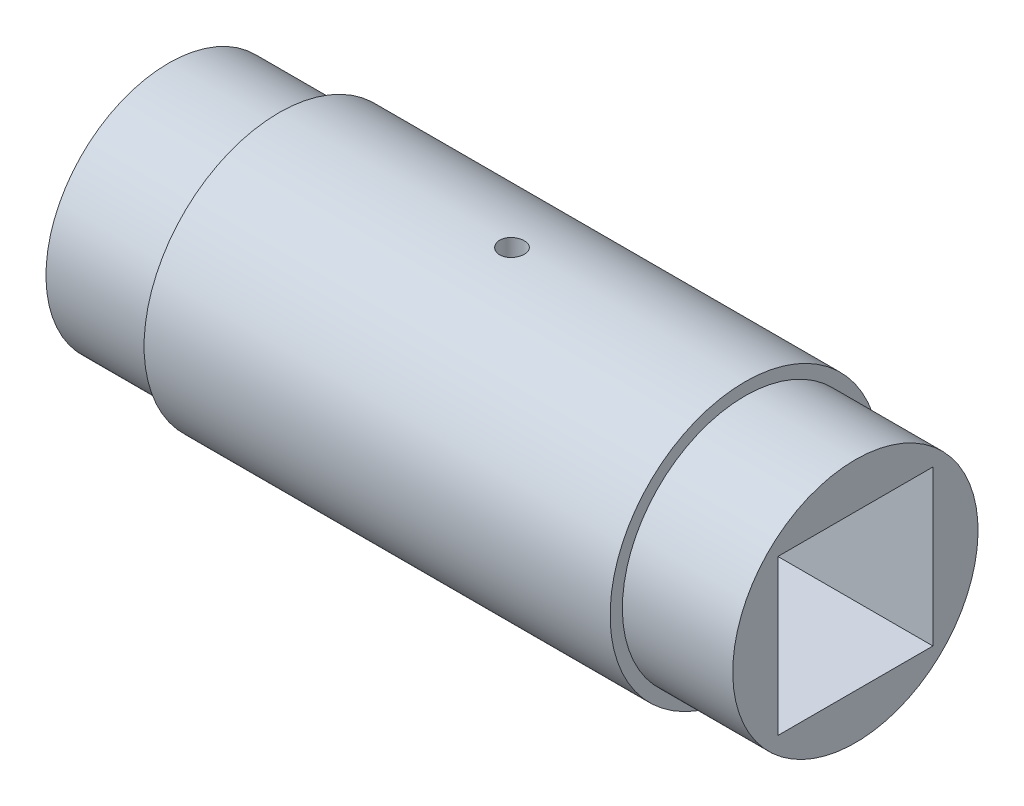
SolidWorks part; units mm, degrees
ref_plane "Front Plane" through (0, 0, 0) normal (0, 0, 1) x (1, 0, 0)
ref_plane "Top Plane" through (0, 0, 0) normal (0, 1, 0) x (1, 0, 0)
ref_plane "Right Plane" through (0, 0, 0) normal (1, 0, 0) x (0, 0, -1)
sketch "Sketch1" plane through (0, 0, 0) normal (0, 0, 1) x (1, 0, 0)
  line L1 (-9.5, 5.5) -> (9.5, 5.5)
  line L2 (-9.5, 5.5) -> (-9.5, 5)
  line L3 (-14, 0) -> (14, 0)
  line L4 (9.5, 5.5) -> (9.5, 5)
  line L6 (-9.5, 5) -> (-14, 5)
  line L7 (-14, 5) -> (-14, 0)
  line L8 (9.5, 5) -> (14, 5)
  line L9 (14, 5) -> (14, 0)
  line L10 (-9.5, 5) -> (9.5, 5) construction
  line L11 (0, 0) -> (-17.9599, 0) construction
  line L12 (-14, 3.16) -> (14, 3.16) construction
  line L13 (0, 0) -> (0, 12.0689) construction
  line L14 (-7, 5.5) -> (-7, 0) construction
  dimension "D1" = 6.32
  dimension "D2" = 10
  dimension "D3" = 28
  dimension "D4" = 19
revolve "Revolve1" add sketch "Sketch1" angle 360 about L11
sketch "Sketch2" plane through (-14, 0, 0) normal (-1, 0, 0) x (0, 0, 1)
  line L0 (0, 0) -> (0, 4.1785) construction
  line L1 (-3.16, 3.16) -> (3.16, 3.16)
  line L2 (-3.16, 3.16) -> (-3.16, -3.16)
  line L3 (-3.16, -3.16) -> (3.16, -3.16)
  line L4 (3.16, 3.16) -> (3.16, -3.16)
  line L5 (0, 0) -> (3.8262, 0) construction
extrude "Cut-Extrude1" cut sketch "Sketch2" against normal through all
sketch "Sketch3" plane through (0, 0, 0) normal (0, 1, 0) x (1, 0, 0)
  circle A0 centre (0, 0) radius 0.5
  circle A1 centre (0, 0) radius 0.5 construction
extrude "Cut-Extrude2" cut sketch "Sketch3" along normal through all
